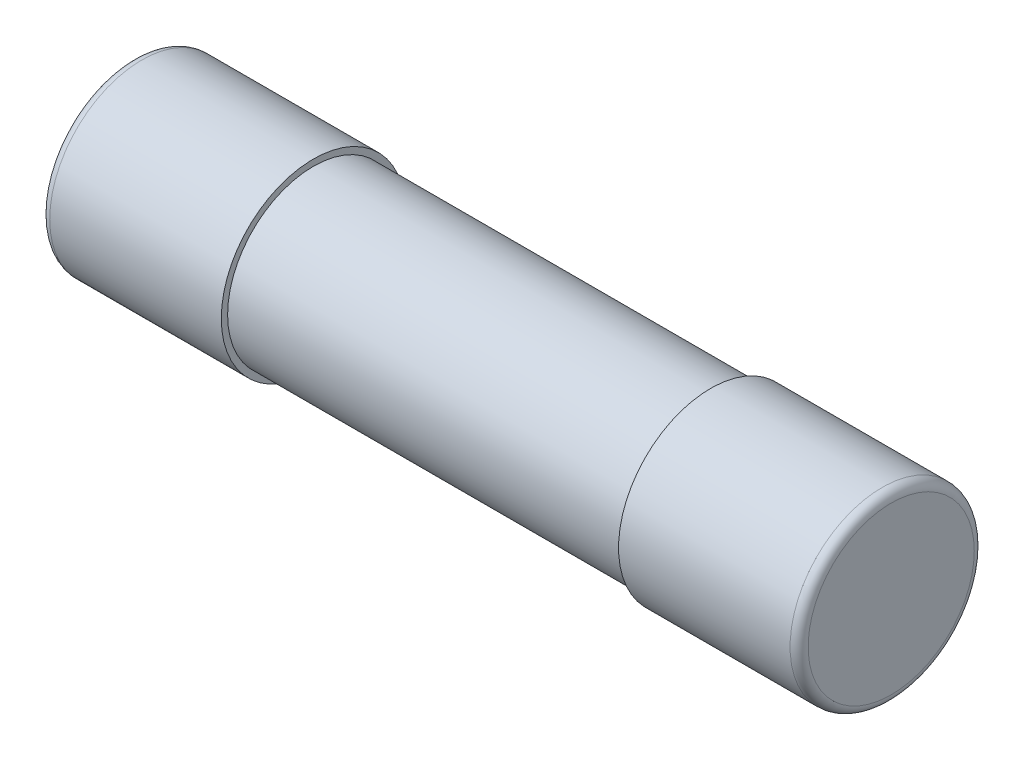
SolidWorks part; units mm, degrees
ref_plane "Front Plane" through (0, 0, 0) normal (0, 0, 1) x (1, 0, 0)
ref_plane "Top Plane" through (0, 0, 0) normal (0, 1, 0) x (1, 0, 0)
ref_plane "Right Plane" through (0, 0, 0) normal (1, 0, 0) x (0, 0, -1)
sketch "Sketch1" plane through (0, 0, 0) normal (1, 0, 0) x (0, 0, -1)
  circle A0 centre (0, 0) radius 2.375
  dimension "D1" = 4.75
extrude "Extrude1" add sketch "Sketch1" along normal mid plane 20
shell "Shell1" thickness 0.2
sketch "Sketch2" plane through (0, 0, 0) normal (1, 0, 0) x (0, 0, -1)
  circle A0 centre (0, 0) radius 0.05
extrude "Extrude2" add sketch "Sketch2" along normal blind 9.65 and the other way blind 9.65 separate body
ref_plane "Plane1" through (10.5, 0, 0) normal (1, 0, 0) x (0, 0, -1)
sketch "Sketch7" plane through (10.5, 0, 0) normal (1, 0, 0) x (0, 0, -1)
  circle A0 centre (0, 0) radius 2.55
  dimension "D1" = 5.1
extrude "Extrude6" add sketch "Sketch7" against normal blind 5
fillet "Fillet2" radius 0.25 1 edges at (10.5, 0, -2.55)
ref_plane "Plane2" through (-10.5, 0, 0) normal (-1, 0, 0) x (0, 0, 1)
sketch "Sketch8" plane through (-10.5, 0, 0) normal (-1, 0, 0) x (0, 0, 1)
  circle A0 centre (0, 0) radius 2.55
  dimension "D1" = 5.1
extrude "Extrude7" add sketch "Sketch8" against normal blind 5
fillet "Fillet3" radius 0.25 1 edges at (-10.5, 0, 2.55)
